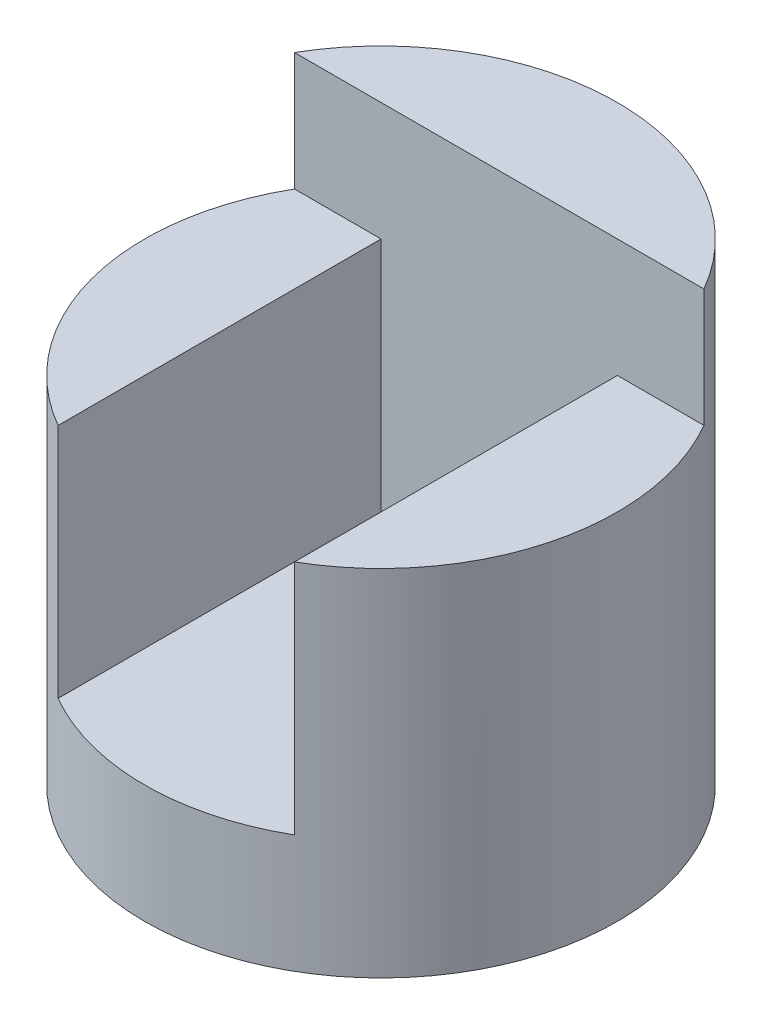
SolidWorks part; units mm, degrees
ref_plane "Front" through (0, 0, 0) normal (0, 0, 1) x (1, 0, 0)
ref_plane "Top" through (0, 0, 0) normal (0, 1, 0) x (1, 0, 0)
ref_plane "Right" through (0, 0, 0) normal (1, 0, 0) x (0, 0, -1)
sketch "Sketch1" plane through (0, 0, 0) normal (0, 1, 0) x (1, 0, 0)
  circle A0 centre (0, 0) radius 2
  dimension "D1" = 4
extrude "Boss-Extrude1" add sketch "Sketch1" along normal blind 4
sketch "Sketch2" plane through (0, 0, 0) normal (0, 0, 1) x (1, 0, 0)
  line L0 (-2, 4) -> (2, 4)
  line L1 (2, 4) -> (2, 3)
  line L2 (2, 0) -> (2, 4) construction
  line L3 (2, 3) -> (1, 3)
  line L4 (1, 3) -> (1, 1)
  line L5 (1, 1) -> (-1, 1)
  line L6 (-1, 1) -> (-1, 3)
  line L7 (-1, 3) -> (-2, 3)
  line L8 (-2, 3) -> (-2, 4)
  dimension "D1" = 1
  dimension "D2" = 1
  dimension "D3" = 1
  dimension "D4" = 1
  dimension "D5" = 2
extrude "Cut-Extrude1" cut sketch "Sketch2" against normal blind 1 and the other way blind 3
